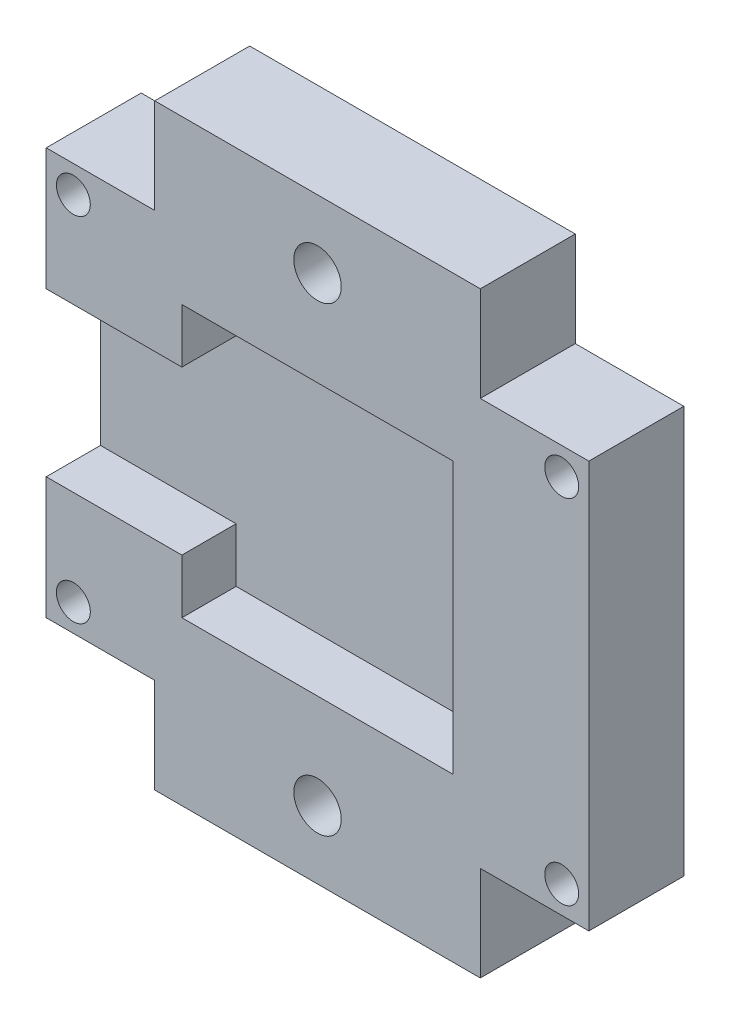
SolidWorks part; units mm, degrees
ref_plane "Front Plane" through (0, 0, 0) normal (0, 0, 1) x (1, 0, 0)
ref_plane "Top Plane" through (0, 0, 0) normal (0, 1, 0) x (1, 0, 0)
ref_plane "Right Plane" through (0, 0, 0) normal (1, 0, 0) x (0, 0, -1)
sketch "Sketch1" plane through (0, 0, 0) normal (0, 0, 1) x (1, 0, 0)
  line L1 (0, 0) -> (40, 0)
  line L2 (0, 0) -> (0, 30)
  line L3 (0, 30) -> (40, 30)
  line L4 (40, 0) -> (40, 30)
  dimension "D1" = 30
  dimension "D2" = 40
extrude "Boss-Extrude1" add sketch "Sketch1" along normal blind 7
sketch "Sketch2" plane through (0, 0, 7) normal (0, 0, 1) x (1, 0, 0)
  line L0 (0, 30) -> (0, 0) construction
  line L1 (10, 25) -> (30, 25)
  line L2 (10, 25) -> (10, 5)
  line L3 (10, 5) -> (30, 5)
  line L4 (30, 25) -> (30, 5)
  point P4 (10, 15)
  point P7 (0, 15)
  dimension "D1" = 20
  dimension "D2" = 20
  dimension "D3" = 10
extrude "Cut-Extrude1" cut sketch "Sketch2" against normal blind 4
sketch "Sketch3" plane through (0, 0, 0) normal (-1, 0, 0) x (0, 0, 1)
  line L0 (7, 30) -> (7, 0) construction
  line L1 (7, 21) -> (3, 21)
  line L2 (7, 21) -> (7, 9)
  line L3 (7, 9) -> (3, 9)
  line L4 (3, 21) -> (3, 9)
  line L5 (7, 30) -> (0, 30) construction
  point P8 (5, 21)
  dimension "D1" = 4
  dimension "D2" = 9
  dimension "D3" = 12
extrude "Cut-Extrude2" cut sketch "Sketch3" against normal blind 26
sketch "Sketch4" plane through (0, 0, 7) normal (0, 0, 1) x (1, 0, 0)
  line L0 (20, 30) -> (20, 23.8123) construction
  line L1 (40, 30) -> (0, 30) construction
  line L2 (0, 15) -> (11.3473, 15) construction
  line L3 (0, 21) -> (0, 9) construction
  circle A0 centre (2, 28) radius 1.25
  circle A1 centre (38, 28) radius 1.25
  circle A2 centre (38, 2) radius 1.25
  circle A3 centre (2, 2) radius 1.25
  dimension "D1" = 2.5
  dimension "D2" = 36
  dimension "D3" = 26
extrude "Cut-Extrude3" cut sketch "Sketch4" against normal through all
sketch "Sketch5" plane through (0, 0, 7) normal (0, 0, 1) x (1, 0, 0)
  line L0 (40, 30) -> (0, 30) construction
  line L1 (8, 30) -> (32, 30)
  line L2 (8, 30) -> (8, 37)
  line L3 (8, 37) -> (32, 37)
  line L4 (32, 30) -> (32, 37)
  line L5 (0, 15) -> (14.6418, 15) construction
  line L6 (0, 21) -> (0, 9) construction
  line L7 (32, 0) -> (32, -7)
  line L8 (8, 0) -> (32, 0)
  line L9 (8, -7) -> (32, -7)
  line L10 (8, 0) -> (8, -7)
  point P6 (20, 30)
  point P7 (20, 30)
  dimension "D1" = 12
  dimension "D2" = 7
extrude "Boss-Extrude2" add sketch "Sketch5" against normal blind 7
sketch "Sketch6" plane through (0, 0, 7) normal (0, 0, 1) x (1, 0, 0)
  line L0 (10, 5) -> (30, 5) construction
  line L1 (0, 21) -> (0, 9) construction
  line L2 (0, 15) -> (21.7554, 15) construction
  circle A0 centre (20, -2) radius 1.75
  circle A1 centre (20, 32) radius 1.75
  point P4 (20, 5)
  point P7 (0, 15)
  dimension "D1" = 3.5
  dimension "D2" = 17
extrude "Cut-Extrude4" cut sketch "Sketch6" against normal through all
